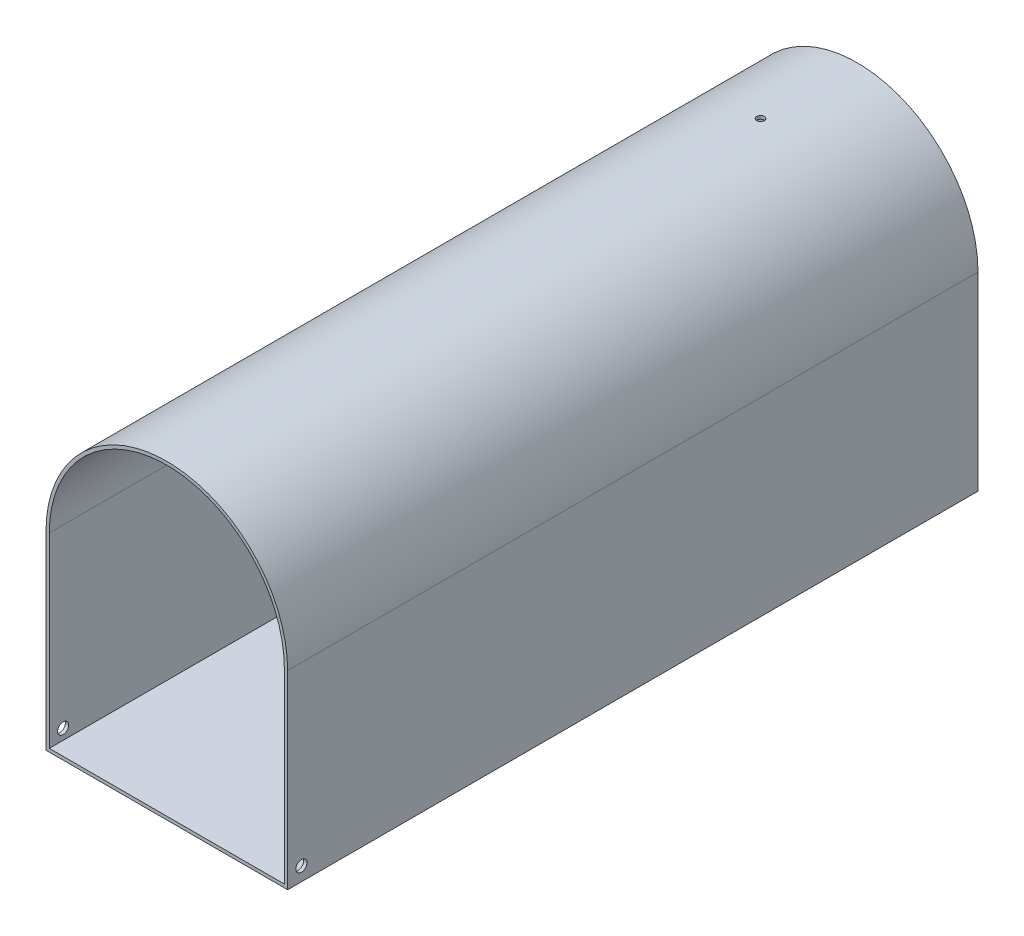
SolidWorks part; units mm, degrees
ref_plane "Front Plane" through (0, 0, 0) normal (0, 0, 1) x (1, 0, 0)
ref_plane "Top Plane" through (0, 0, 0) normal (0, 1, 0) x (1, 0, 0)
ref_plane "Right Plane" through (0, 0, 0) normal (1, 0, 0) x (0, 0, -1)
sketch "Sketch1" plane through (0, 0, 0) normal (0, 0, 1) x (1, 0, 0)
  line L1 (0, 0) -> (175, 0)
  line L2 (0, 0) -> (0, 137.5)
  line L4 (175, 0) -> (175, 137.5)
  arc A0 (175, 137.5) -> (0, 137.5) centre (87.5, 137.5) ccw
  point P7 (87.5, 225)
  dimension "D1" = 175
  dimension "D2" = 225
extrude "Boss-Extrude1" add sketch "Sketch1" along normal blind 500 contours A0 L2 L1 L4
sketch "Sketch2" plane through (0, 0, 500) normal (0, 0, 1) x (1, 0, 0)
  line L6 (172.6187, 2.3812) -> (172.6187, 137.5)
  line L7 (2.3812, 2.3812) -> (172.6187, 2.3812)
  line L8 (2.3813, 137.5) -> (2.3812, 2.3812)
  line L9 (172.6187, 2.3812) -> (172.6187, 137.5)
  line L10 (2.3812, 2.3812) -> (172.6187, 2.3812)
  line L11 (2.3813, 137.5) -> (2.3812, 2.3812)
  arc A2 (172.6187, 137.5) -> (2.3813, 137.5) centre (87.5, 137.5) ccw
  arc A3 (172.6187, 137.5) -> (2.3813, 137.5) centre (87.5, 137.5) ccw
  dimension "D1" = 2.3813
extrude "Cut-Extrude1" cut sketch "Sketch2" against normal blind 497
sketch "Sketch3" plane through (175, 0, 0) normal (1, 0, 0) x (0, 0, -1)
  line L0 (-500, 0) -> (0, 0) construction
  line L1 (-500, 0) -> (-500, 137.5) construction
  circle A0 centre (-490, 10) radius 4
  dimension "D3" = 8
  dimension "D1" = 10
  dimension "D2" = 10
extrude "Cut-Extrude2" cut sketch "Sketch3" against normal blind 497
ref_plane "Plane1" through (0, 225, 0) normal (0, 1, 0) x (1, 0, 0)
sketch "Sketch4" plane through (0, 225, 0) normal (0, 1, 0) x (1, 0, 0)
  line L0 (87.5, 0) -> (87.5, -500) construction
  line L1 (175, 0) -> (0, 0) construction
  line L2 (0, -500) -> (175, -500) construction
  circle A0 centre (87.5, -70) radius 2.75
  dimension "D1" = 5.5
  dimension "D2" = 70
extrude "Cut-Extrude3" cut sketch "Sketch4" against normal blind 5
